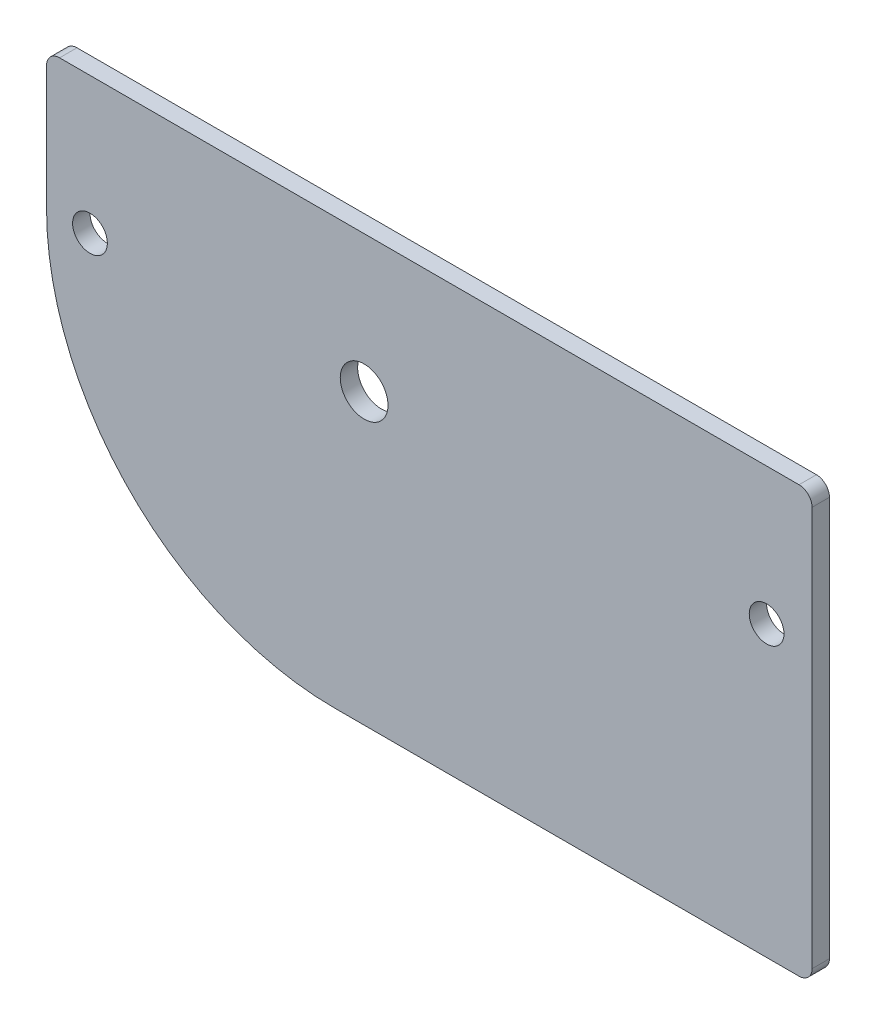
SolidWorks part; units mm, degrees
ref_plane "Front Plane" through (0, 0, 0) normal (0, 0, 1) x (1, 0, 0)
ref_plane "Top Plane" through (0, 0, 0) normal (0, 1, 0) x (1, 0, 0)
ref_plane "Right Plane" through (0, 0, 0) normal (1, 0, 0) x (0, 0, -1)
sketch "Sketch1" plane through (0, 0, 0) normal (0, 0, 1) x (1, 0, 0)
  line L1 (58.5349, 30.4647) -> (-58.5349, 30.4647)
  line L2 (58.5349, 30.4647) -> (58.5349, -30.4647)
  line L3 (58.5349, -30.4647) -> (-58.5349, -30.4647)
  line L4 (-58.5349, 30.4647) -> (-58.5349, -30.4647)
  line L5 (58.5349, 30.4647) -> (-58.5349, -30.4647) construction
  line L6 (58.5349, -30.4647) -> (-58.5349, 30.4647) construction
  point P0 (0, 0)
extrude "Boss-Extrude1" add sketch "Sketch1" along normal blind 2
sketch "Sketch3" plane through (0, 0, 0) normal (0, 0, -1) x (-1, 0, 0)
  line L1 (25.3499, -30.4647) -> (25.3499, -36.7567)
  line L2 (-29.5914, 17.0353) -> (-29.5914, -28.9647)
  line L4 (58.5349, 30.4647) -> (58.5349, 17.0353)
  line L5 (25.3499, -36.7567) -> (60.4942, -36.7567)
  line L6 (-58.5349, -30.4647) -> (-58.5349, 30.4647)
  line L9 (60.4942, -36.7567) -> (60.4942, 2.7953)
  line L10 (57.0349, 18.5353) -> (-28.0914, 18.5353)
  line L11 (60.4942, 2.7953) -> (58.5349, 2.7953)
  line L12 (53.5349, 2.7946) -> (-51.4007, 2.7946) construction
  line L14 (-58.5349, 30.4647) -> (58.5349, 30.4647)
  line L22 (-58.5349, -30.4647) -> (-28.0914, -30.4647)
  circle A0 centre (-24.3575, 2.7946) radius 2
  arc A1 (25.3499, -30.4647) -> (58.5349, 2.7953) centre (25.3499, 2.7203) ccw
  arc A3 (58.5349, 17.0353) -> (57.0349, 18.5353) centre (57.0349, 17.0353) ccw
  circle A4 centre (53.5349, 2.7946) radius 2
  circle A5 centre (21.9749, 2.7953) radius 2.75
  arc A6 (-28.0914, 18.5353) -> (-29.5914, 17.0353) centre (-28.0914, 17.0353) ccw
  arc A7 (-29.5914, -28.9647) -> (-28.0914, -30.4647) centre (-28.0914, -28.9647) ccw
extrude "Cut-Extrude1" cut sketch "Sketch3" against normal through all
